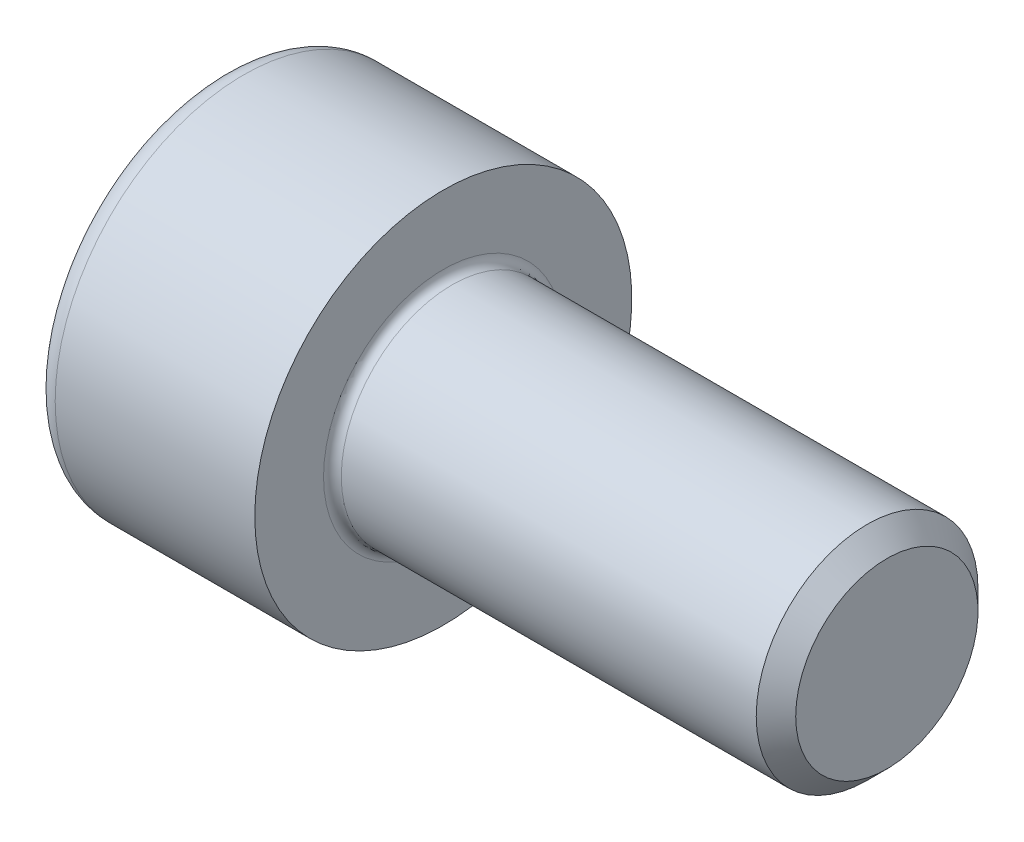
SolidWorks part; units mm, degrees
revolve "Base-Revolve" add sketch "BodySke"
sketch "BodySke" plane through (0, 0, 0) normal (0, 0, 1) x (1, 0, 0)
  line L0 (0, 0) -> (0, 4.25)
  line L1 (0, 4.25) -> (5, 4.25)
  line L2 (5, 4.25) -> (5, 2.5)
  line L3 (5, 2.5) -> (14.555, 2.5)
  line L4 (15, 2.055) -> (15, 0)
  line L5 (15, 0) -> (0, 0)
  line L6 (-31.75, 0) -> (127, 0) construction
  line L8 (15, 2.055) -> (14.555, 2.5)
  line L10 (15, -2.055) -> (14.555, -2.5) construction
  line L11 (5.8, 9.525) -> (5.8, 3.175) construction
  line L12 (5, 9.525) -> (5, 3.175) construction
  line L13 (-45, 9.525) -> (-45, 3.175) construction
  dimension "Head_ht" = 5
  dimension "Length" = 10
  dimension "Body_ch_ang" = 45
  dimension "Diameter" = 5
  dimension "Minor_dia" = 4.11
  dimension "Advance" = 0.8
  dimension "Thread_nom" = 10
  dimension "Thread_length" = 60
  dimension "Head_dia" = 8.5
cosmetic thread "ThreadCosmetic"
fillet "Fillet1" radius 0.2 1 edges at (5, 0, 2.5)
fillet "Fillet2" radius 0.5 1 edges at (0, 0, 4.25)
ref_plane "Plane1" through (0, 0, 0) normal (0, 0, 1) x (1, 0, 0)
ref_plane "Plane2" through (0, 0, 0) normal (0, 1, 0) x (1, 0, 0)
ref_plane "Plane3" through (0, 0, 0) normal (1, 0, 0) x (0, 0, -1)
other "Configuration Table"
sketch "Sketch2" plane through (0, 0, 0) normal (0, 0, 1) x (1, 0, 0)
  line L0 (0, 2.01) -> (2.5, 2.01)
  line L1 (2.5, 2.01) -> (3.6605, 0)
  line L2 (-31.75, 0) -> (127, 0) construction
  line L3 (3.6605, 0) -> (0, 0)
  line L4 (0, 0) -> (0, 2.01)
  line L6 (0, 0) -> (47.625, 0) construction
  dimension "D1" = 2.01
  dimension "D2" = 60
  dimension "Depth" = 2.5
revolve "Hex-PreBroach" cut sketch "Sketch2" angle 360 about L6
sketch "Sketch3" plane through (0, 0, 0) normal (-1, 0, 0) x (0, 0.5, 0.866)
  line L0 (1.1605, 2.01) -> (-1.1605, 2.01)
  line L1 (-1.1605, 2.01) -> (-2.3209, 0)
  line L2 (1.1605, 2.01) -> (2.3209, 0)
  line L3 (1.1605, -2.01) -> (2.3209, 0)
  line L4 (1.1605, -2.01) -> (-1.1605, -2.01)
  line L5 (-1.1605, -2.01) -> (-2.3209, 0)
  dimension "D1" = 2.01
  dimension "D2" = 2.01
  dimension "Hex_size" = 4.02
extrude "Hex" cut sketch "Sketch3" against normal blind 2.5
sketch "ThdSchSke" plane through (0, 0, 0) normal (0, 0, 1) x (1, 0, 0)
  line L0 (7.4, -2.055) -> (7.0884, -2.5)
  line L1 (7.4, -2.055) -> (7.7116, -2.5)
  line L2 (7.7116, -2.5) -> (7.7116, -3.125)
  line L3 (-3.175, 0) -> (5.1513, 0) construction
  line L4 (0, 3.75) -> (0, -3.75) construction
  line L5 (7.7116, -3.125) -> (7.0884, -3.125)
  line L6 (7.0884, -3.125) -> (7.0884, -2.5)
  dimension "Thread_minor" = 4.11
  dimension "Diameter" = 5
  dimension "Start" = 7.4
revolve "ThreadSchematic" [suppressed] cut sketch "ThdSchSke" angle 360 about L3
pattern_linear "ThdSchPat" [suppressed]
equation "\"D2@Sketch3\" = \"Hex_size@Sketch3\" / 2"
equation "\"D1@Sketch3\" = \"Hex_size@Sketch3\" / 2"
equation "\"D1@Sketch2\" = \"Hex_size@Sketch3\" / 2"
equation "\"Thread_minor@ThreadCosmetic\"  =  \"Minor_dia@BodySke\""
equation "\"Depth@Sketch2\" =  \"Key_eng@Hex\""
equation "\"Thread_length@ThreadCosmetic\" = ((sgn( (\"Length@BodySke\" - \"Advance@BodySke\" * 3.0) - \"Thread_nom@BodySke\" )-1)*( (\"Length@BodySke\" - \"Advance@BodySke\" * 3.0) - \"Thread_nom@BodySke\" ))/-2+ \"Thread_nom@BodySke\""
equation "\"Thread_minor@ThdSchSke\" = \"Minor_dia@BodySke\""
equation "\"Diameter@ThdSchSke\" = \"Diameter@BodySke\""
equation "\"Overcut@ThdSchSke\" = \"Diameter@BodySke\" * 1.25"
equation "\"Start@ThdSchSke\" = \"Head_ht@BodySke\" + \"Length@BodySke\" - \"Thread_length@ThreadCosmetic\"  '---Non-countersunk---"
equation "\"Num_threads@ThdSchPat\" = int( \"Thread_length@ThreadCosmetic\" / \"Advance@BodySke\" + 0.999 )  + 1"
equation "\"Advance@ThdSchPat\" = \"Thread_length@ThreadCosmetic\" /  (\"Num_threads@ThdSchPat\" - 1) 'relax it"
equation "\"Num_threads@ThdSchPat\" = \"Num_threads@ThdSchPat\" - sgn( \"Num_threads@ThdSchPat\" - 1) '---chamfered tips only---"
